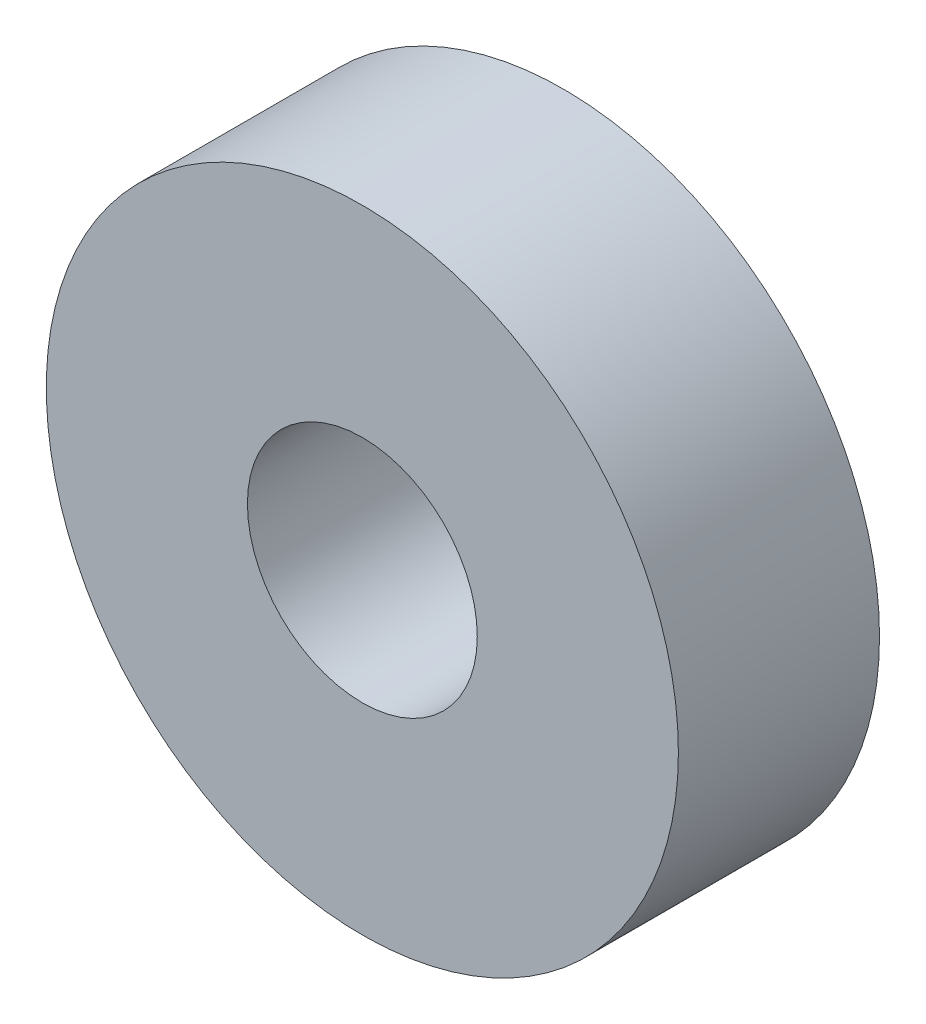
SolidWorks part; units mm, degrees
ref_plane "Front Plane" through (0, 0, 0) normal (0, 0, 1) x (1, 0, 0)
ref_plane "Top Plane" through (0, 0, 0) normal (0, 1, 0) x (1, 0, 0)
ref_plane "Right Plane" through (0, 0, 0) normal (1, 0, 0) x (0, 0, -1)
sketch "Sketch1" plane through (0, 0, 0) normal (0, 0, 1) x (1, 0, 0)
  circle A0 centre (0, 0) radius 11
  circle A1 centre (0, 0) radius 4
  dimension "D1" = 22
  dimension "D2" = 8
extrude "Boss-Extrude1" add sketch "Sketch1" along normal blind 7
scale "Scale1" scale about centroid uniform scaling yes scale factor 0.571429
